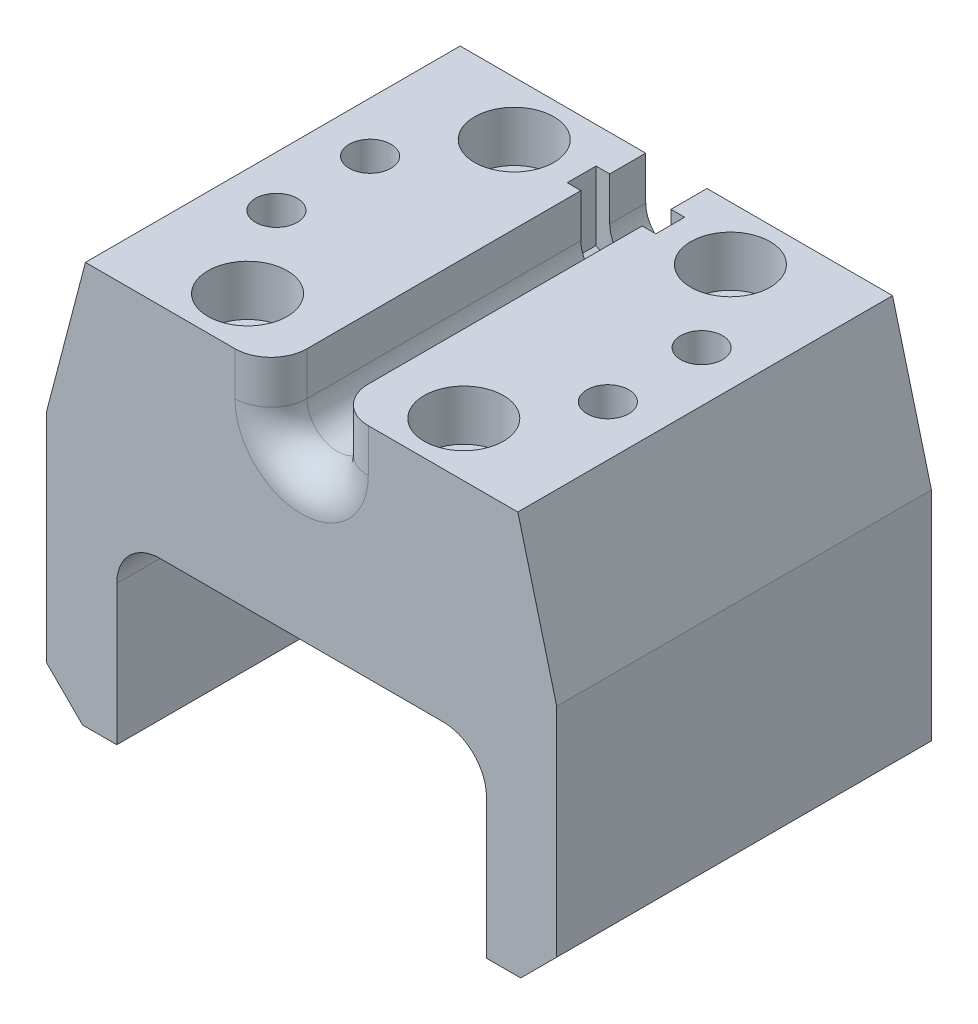
SolidWorks part; units mm, degrees
material "PET"
ref_plane "Front Plane" through (0, 0, 0) normal (0, 0, 1) x (1, 0, 0)
ref_plane "Top Plane" through (0, 0, 0) normal (0, 1, 0) x (1, 0, 0)
ref_plane "Right Plane" through (0, 0, 0) normal (1, 0, 0) x (0, 0, -1)
sketch "Sketch1" plane through (0, 0, 0) normal (0, 0, 1) x (1, 0, 0)
  line L0 (0, 19.0297) -> (0, -2.5925) construction
  line L1 (-12.9623, 0) -> (13.1829, 0) construction
  line L2 (35.4, 6) -> (-35.4, 6)
  line L3 (-35.4, 6) -> (-35.4, -49.8)
  line L4 (-35.4, -49.8) -> (-25.65, -49.8)
  line L5 (-25.65, -49.8) -> (-25.65, -24.4)
  line L6 (-25.65, -24.4) -> (25.65, -24.4)
  line L7 (35.4, -49.8) -> (25.65, -49.8)
  line L8 (25.65, -49.8) -> (25.65, -24.4)
  line L9 (35.4, 6) -> (35.4, -49.8)
  circle A0 centre (0, 0) radius 3.75 construction
  point P16 (0, -24.4)
  point P17 (0, 6)
  dimension "D1" = 7.5
  dimension "D2" = 6
  dimension "D5" = 51.3
  dimension "D6" = 24.4
  dimension "D3" = 70.8
  dimension "D4" = 25.4
extrude "Boss-Extrude1" add sketch "Sketch1" along normal mid plane 52
sketch "Sketch9" plane through (0, 0, 26) normal (0, 0, 1) x (1, 0, 0)
  line L0 (0, 0) -> (0, -24.4) construction
  line L1 (-25.65, -24.4) -> (25.65, -24.4) construction
  line L2 (-30, 6) -> (-35.4, -14.65)
  line L3 (35.4, 6) -> (-35.4, 6) construction
  line L4 (-35.4, 6) -> (-35.4, -49.8) construction
  line L5 (-35.4, -14.65) -> (-35.4, 6)
  line L6 (-35.4, 6) -> (-30, 6)
  line L7 (-25.65, -24.4) -> (-35.4, -24.4) construction
  line L8 (-35.4, -24.4) -> (-35.4, -14.65) construction
  line L9 (35.4, 6) -> (30, 6)
  line L10 (35.4, -14.65) -> (35.4, 6)
  line L11 (30, 6) -> (35.4, -14.65)
  dimension "D1" = 30
extrude "Cut-Extrude8" cut sketch "Sketch9" against normal through all
fillet "Fillet1" radius 6 2 edges at (25.65, -24.4, 0) (-25.65, -24.4, 0)
sketch "Sketch2" plane through (0, 6, 0) normal (0, 1, 0) x (1, 0, 0)
  line L0 (0, 35.9356) -> (0, 6.1551) construction
  line L1 (-23, 6.5) -> (-23, -6.5) construction
  line L3 (30, 26) -> (-30, 26) construction
  line L7 (0, 0) -> (-35.4, 0) construction
  line L8 (-35.4, 26) -> (-35.4, -26) construction
  circle A2 centre (-23, 6.5) radius 2.9
  circle A3 centre (-23, -6.5) radius 2.9
  circle A4 centre (-15, 18.5) radius 3.05
  circle A5 centre (23, -6.5) radius 2.9
  circle A6 centre (23, 6.5) radius 2.9
  circle A7 centre (15, 18.5) radius 3.05
  circle A8 centre (15, -18.5) radius 3.05
  circle A9 centre (-15, -18.5) radius 3.05
  dimension "D2" = 5.8
  dimension "D3" = 12
  dimension "D4" = 6.1
  dimension "D5" = 13
  dimension "D6" = 23
  dimension "D9" = 7.5
  dimension "D10" = 15
extrude "Cut-Extrude1" cut sketch "Sketch2" against normal blind 29
sketch "Sketch3" plane through (0, 6, 0) normal (0, 1, 0) x (1, 0, 0)
  circle A0 centre (-15, 18.5) radius 5.5
  circle A1 centre (15, 18.5) radius 5.5
  circle A2 centre (-15, -18.5) radius 5.5
  circle A3 centre (15, -18.5) radius 5.5
  dimension "D1" = 11
extrude "Cut-Extrude2" cut sketch "Sketch3" against normal blind 7
chamfer "Chamfer2" distance 5 angle 45 2 edges at (-35.4, -49.8, 0) (35.4, -49.8, 0)
sketch "Sketch10" plane through (0, 0, -26) normal (0, 0, -1) x (-1, 0, 0)
  line L1 (-4.25, 0) -> (-4.25, 11.4915)
  line L2 (-4.25, 11.4915) -> (4.25, 11.4915)
  line L3 (4.25, 11.4915) -> (4.25, 0)
  arc A0 (-4.25, 0) -> (4.25, 0) centre (0, 0) ccw
  dimension "D1" = 8.5
extrude "Cut-Extrude9" cut sketch "Sketch10" against normal through all
sketch "Sketch11" plane through (0, 0, -26) normal (0, 0, -1) x (-1, 0, 0)
  line L0 (-6.15, 3.5507) -> (-6.15, 9.9104)
  line L1 (-6.15, 3.5507) -> (-6.15, -3.5507)
  line L2 (-6.15, -3.5507) -> (0, -7.1014)
  line L3 (0, -7.1014) -> (6.15, -3.5507)
  line L4 (6.15, -3.5507) -> (6.15, 3.5507)
  line L5 (6.15, 3.5507) -> (0, 7.1014) construction
  line L6 (0, 7.1014) -> (-6.15, 3.5507) construction
  line L7 (-6.15, 9.9104) -> (6.15, 9.9104)
  line L8 (6.15, 9.9104) -> (6.15, 3.5507)
  circle A0 centre (0, 0) radius 6.15 construction
  dimension "D1" = 12.3
extrude "Cut-Extrude10" cut sketch "Sketch11" against normal blind 4 from offset 5 offset against normal yes
fillet "Fillet2" radius 5 3 edges at (4.25, 3, 26) (-4.25, 3, 26) (0, -4.25, 26)
sketch "Sketch12" plane through (0, -23, 0) normal (0, 1, 0) x (1, 0, 0)
  circle A0 centre (-15, 18.5) radius 3.05 construction
  circle A1 centre (15, 18.5) radius 3.05 construction
  circle A2 centre (15, -18.5) radius 3.05 construction
  circle A3 centre (-15, -18.5) radius 3.05 construction
  circle A4 centre (-15, 18.5) radius 3.05
  circle A5 centre (15, 18.5) radius 3.05
  circle A6 centre (15, -18.5) radius 3.05
  circle A7 centre (-15, -18.5) radius 3.05
extrude "Cut-Extrude11" cut sketch "Sketch12" against normal blind 4
fillet "Fillet3" radius 2 4 edges at (-25.9, -23, -6.5) (-25.9, -23, 6.5) (25.9, -23, -6.5) (25.9, -23, 6.5)
equation "\"M5_tap\"=4.2mm\t\t\t\t\t\t\t' Below you can do mesurements as follows: cm, mm, ft, in, m, "
equation "\"M5_clearence\"=5.5mm"
equation "\"M6_tap\"=5mm"
equation "\"M6_clearence\"=6.6mm"
equation "\"work_area_width\"=1100mm"
equation "\"work_area_depth\"=900mm"
equation "\"steel_base_width\"=3in\t"
equation "\"steel_base_height\"=2in"
equation "\"steel_base_wall_thickness\"=0.125in"
equation "\"steel_base_radius\"=6mm"
equation "\"steel_sides_width\"=3in\t\t\t\t\t'this tube is rotated so flip width/height"
equation "\"steel_sides_height\"=2in\t\t\t\t'this tube is rotated so flip width/height"
equation "\"steel_sides_wall_thickness\"=0.125in"
equation "\"steel_sides_radius\"=6mm"
equation "\"steel_gantry_width\"=4in\t\t\t\t'this tube is rotated so flip width/height"
equation "\"steel_gantry_height\"=3in\t\t\t\t'this tube is rotated so flip width/height"
equation "\"steel_gantry_wall_thickness\"=0.125in"
equation "\"steel_gantry_radius\"=6mm"
equation "\"steel_rollers_width\"=3in"
equation "\"steel_rollers_height\"=2in\t\t\t\t'keep as low as possible as this increases how big plastic parts are"
equation "\"steel_rollers_wall_thickness\"=0.125in"
equation "\"steel_rollers_radius\"=6mm"
equation "\"steel_zbox_width\"=4in\t\t\t\t\t'if the gantry height (rotated) is too thick, a wider zbox is necessary"
equation "\"steel_zbox_height\"=2in\t\t\t\t\t'hole patteren changes as the zbox and gantry height (rotated) changes."
equation "\"steel_zbox_wall_thickness\"=0.125in"
equation "\"steel_zbox_radius\"=6mm"
equation "\"alu_zangle_width\"=4in\t\t\t\t\t'check that it doesn't interfer with the gantry"
equation "\"alu_zangle_height\"=4in"
equation "\"alu_zangle_wall_thickness\"=0.375in\t\t\t'check that it doesn't interfer with the gantry"
equation "\"D3@Sketch1\"=\"steel_sides_height\" + 20"
equation "\"D6@Sketch1\"=\"steel_rollers_height\" /2 -1"
equation "\"D4@Sketch1\"=\"steel_sides_width\"/3"
